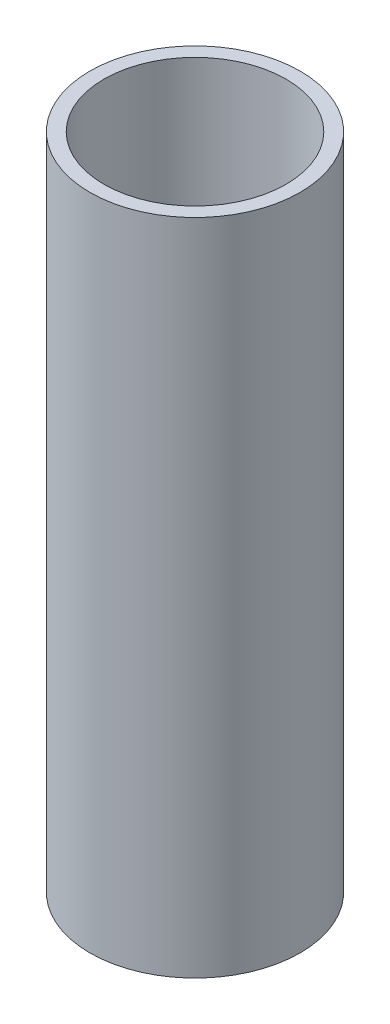
SolidWorks part; units mm, degrees
ref_plane "Front Plane" through (0, 0, 0) normal (0, 0, 1) x (1, 0, 0)
ref_plane "Top Plane" through (0, 0, 0) normal (0, 1, 0) x (1, 0, 0)
ref_plane "Right Plane" through (0, 0, 0) normal (1, 0, 0) x (0, 0, -1)
sketch "Sketch2" plane through (0, 0, 0) normal (0, 0, 1) x (1, 0, 0)
  line L0 (0, 0) -> (0, -100) construction
  line L1 (13, 0) -> (13, -94)
  line L2 (15, 0) -> (15, -94)
  line L3 (13, 0) -> (15, 0)
  line L4 (13, -94) -> (15, -94)
  point P5 (0, 0)
  point P8 (0, 0)
  dimension "D1" = 100
  dimension "D2" = 13
  dimension "D3" = 2
  dimension "D4" = 94
revolve "Revolve2" add sketch "Sketch2" angle 360 about L0
